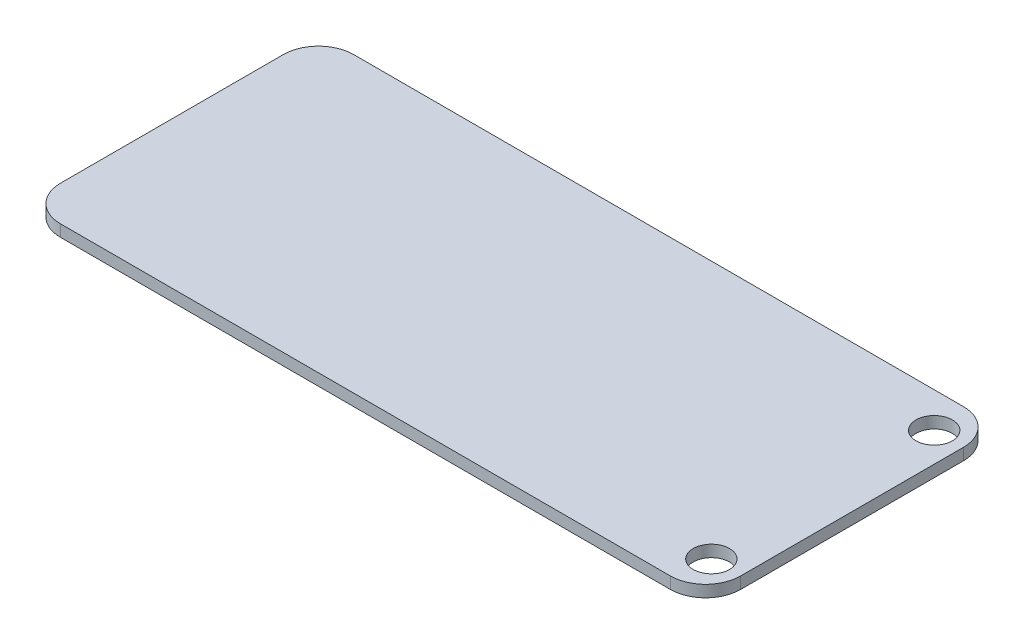
SolidWorks part; units mm, degrees
ref_plane "前视基准面" through (0, 0, 0) normal (0, 0, 1) x (1, 0, 0)
ref_plane "上视基准面" through (0, 0, 0) normal (0, 1, 0) x (1, 0, 0)
ref_plane "右视基准面" through (0, 0, 0) normal (1, 0, 0) x (0, 0, -1)
sketch "草图1" plane through (0, 0, 0) normal (0, 1, 0) x (1, 0, 0)
  line L1 (-29, 12.5) -> (29, 12.5)
  line L2 (-29, 12.5) -> (-29, -12.5)
  line L3 (-29, -12.5) -> (29, -12.5)
  line L4 (29, 12.5) -> (29, -12.5)
  line L5 (-29, 12.5) -> (29, -12.5) construction
  line L6 (-29, -12.5) -> (29, 12.5) construction
  point P0 (0, 0)
  dimension "D1" = 58
  dimension "D2" = 25
extrude "凸台-拉伸1" add sketch "草图1" along normal blind 1
sketch "草图2" plane through (0, 1, 0) normal (0, 1, 0) x (1, 0, 0)
  line L0 (0, 0) -> (16.0692, 0) construction
  line L1 (29, -12.5) -> (29, 12.5) construction
  circle A0 centre (26.5, 9.5) radius 1.55
  circle A1 centre (26.5, -9.5) radius 1.55
  dimension "D1" = 3.1
  dimension "D2" = 19
  dimension "D3" = 2.5
extrude "切除-拉伸1" cut sketch "草图2" against normal through all
fillet "圆角1" radius 3 4 edges at (-29, 0.5, 12.5) (-29, 0.5, -12.5) (29, 0.5, -12.5) (29, 0.5, 12.5)
